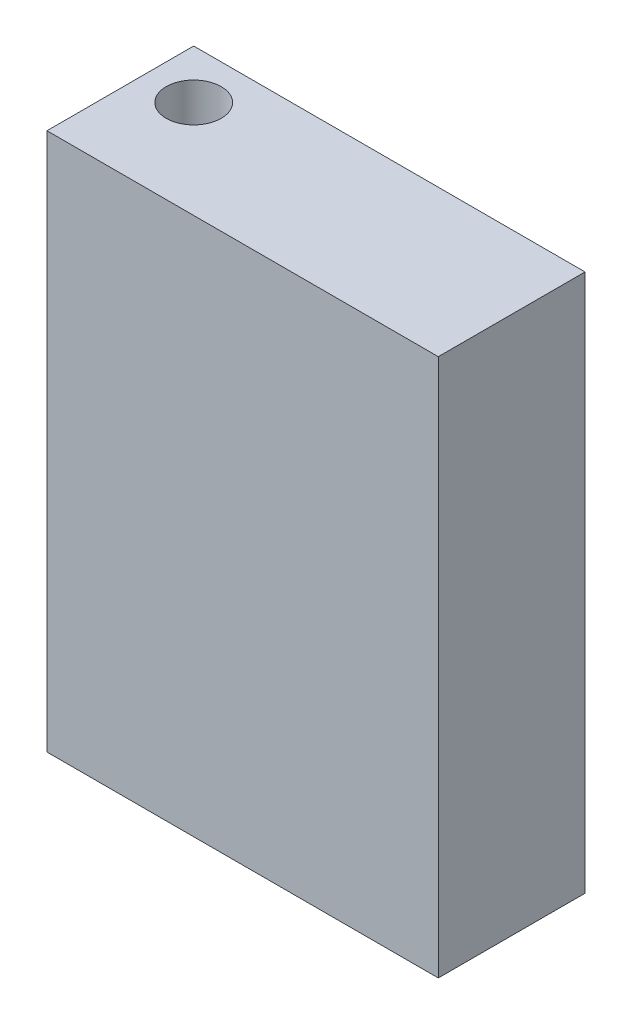
SolidWorks part; units mm, degrees
ref_plane "Front Plane" through (0, 0, 0) normal (0, 0, 1) x (1, 0, 0)
ref_plane "Top Plane" through (0, 0, 0) normal (0, 1, 0) x (1, 0, 0)
ref_plane "Right Plane" through (0, 0, 0) normal (1, 0, 0) x (0, 0, -1)
sketch "Sketch1" plane through (0, 0, 0) normal (0, 0, 1) x (1, 0, 0)
  line L1 (0, 0) -> (50.8, 0)
  line L2 (0, 0) -> (0, 69.85)
  line L3 (0, 69.85) -> (50.8, 69.85)
  line L4 (50.8, 0) -> (50.8, 69.85)
  dimension "D1" = 50.8
  dimension "D2" = 69.85
extrude "Boss-Extrude1" add sketch "Sketch1" along normal blind 19.05
sketch "Sketch2" plane through (0, 69.85, 0) normal (0, 1, 0) x (1, 0, 0)
  line L0 (50.8, 0) -> (0, 0) construction
  line L1 (0, -19.05) -> (0, 0) construction
  circle A0 centre (6.35, -6.35) radius 3.5719
  dimension "D1" = 7.1437
  dimension "D2" = 6.35
  dimension "D3" = 6.35
extrude "Cut-Extrude1" cut sketch "Sketch2" against normal through all
